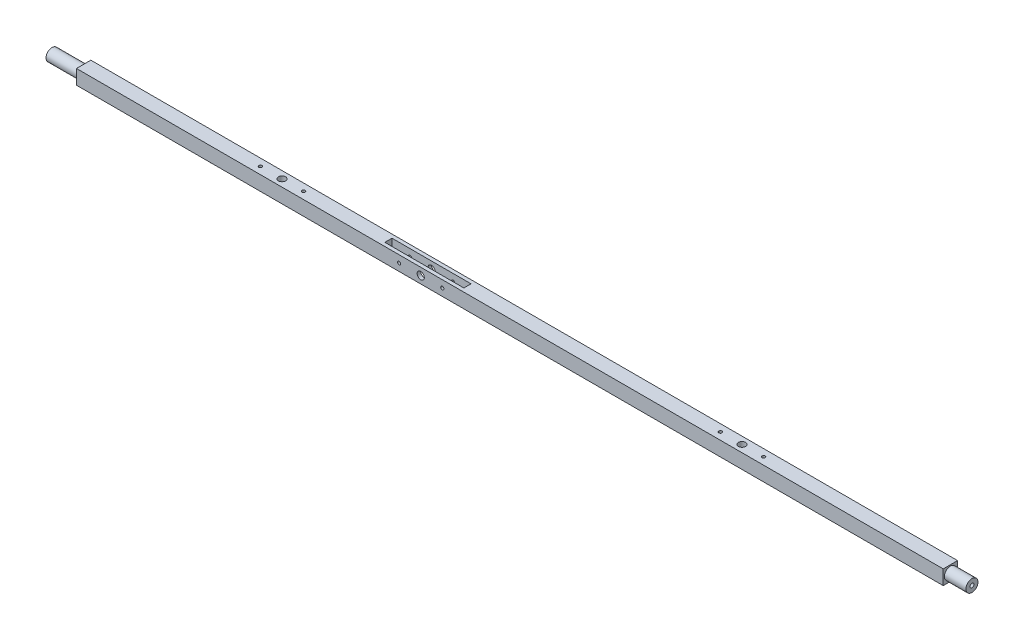
SolidWorks part; units mm, degrees
material "6061-T6 (SS)"
ref_plane "Front Plane" through (0, 0, 0) normal (0, 0, 1) x (1, 0, 0)
ref_plane "Top Plane" through (0, 0, 0) normal (0, 1, 0) x (1, 0, 0)
ref_plane "Right Plane" through (0, 0, 0) normal (1, 0, 0) x (0, 0, -1)
sketch "Sketch1" plane through (0, 0, 0) normal (1, 0, 0) x (0, 0, -1)
  line L1 (-6.35, -6.4107) -> (6.35, -6.4107)
  line L2 (-6.35, -6.4107) -> (-6.35, 6.4107)
  line L3 (-6.35, 6.4107) -> (6.35, 6.4107)
  line L4 (6.35, -6.4107) -> (6.35, 6.4107)
  line L5 (-6.35, -6.4107) -> (6.35, 6.4107) construction
  line L6 (-6.35, 6.4107) -> (6.35, -6.4107) construction
  point P0 (0, 0)
  dimension "D1" = 12.7
  dimension "D2" = 12.8213
extrude "Length" add sketch "Sketch1" along normal mid plane 812.8
ref_plane "Top" through (406.4, 0, 0) normal (1, 0, 0) x (0, 0, -1)
sketch "Sketch2" plane through (406.4, 0, 0) normal (1, 0, 0) x (0, 0, -1)
  line L5 (-3.7537, -3.7896) -> (2.2344, 2.2557) construction
  line L6 (-3.7537, 3.7896) -> (3.7537, -3.7896) construction
  line L7 (-6.35, -6.4107) -> (6.35, -6.4107)
  line L8 (-6.35, -6.4107) -> (-6.35, 6.4107)
  line L9 (-6.35, 6.4107) -> (6.35, 6.4107)
  line L10 (6.35, -6.4107) -> (6.35, 6.4107)
  line L11 (-6.35, -6.4107) -> (6.35, 6.4107) construction
  line L12 (-6.35, 6.4107) -> (6.35, -6.4107) construction
  circle A0 centre (0, 0) radius 5.334
  point P0 (0, 0)
  dimension "D1" = 10.668
extrude "Round Cut 1" cut sketch "Sketch2" against normal blind 19.05 contours L7 L10 L9 L8 A0
ref_plane "Bottom Plane" through (-406.4, 0, 0) normal (-1, 0, 0) x (0, 0, 1)
sketch "Sketch3" plane through (-406.4, 0, 0) normal (-1, 0, 0) x (0, 0, 1)
  line L1 (-6.35, -6.4107) -> (6.35, -6.4107)
  line L2 (-6.35, -6.4107) -> (-6.35, 6.4107)
  line L3 (-6.35, 6.4107) -> (6.35, 6.4107)
  line L4 (6.35, -6.4107) -> (6.35, 6.4107)
  line L5 (-6.35, -6.4107) -> (6.35, 6.4107) construction
  line L6 (-6.35, 6.4107) -> (6.35, -6.4107) construction
  circle A0 centre (0, 0) radius 5.334
  point P0 (0, 0)
  dimension "D1" = 10.668
extrude "Round Cut 2" cut sketch "Sketch3" against normal blind 27.94 contours L1 L4 L3 L2 A0
ref_plane "Plane13" through (0, -6.4107, 0) normal (0, -1, 0) x (-1, 0, 0)
sketch "Sketch9" plane through (0, -6.4107, 0) normal (0, -1, 0) x (-1, 0, 0)
  line L0 (-387.35, 6.35) -> (378.46, 6.35) construction
  line L1 (-279.4, 6.35) -> (-228.6, 6.35)
  line L2 (-279.4, 6.35) -> (-279.4, -6.35)
  line L3 (-279.4, -6.35) -> (-228.6, -6.35)
  line L4 (-228.6, 6.35) -> (-228.6, -6.35)
  line L5 (-387.35, -6.35) -> (378.46, -6.35) construction
  line L6 (-406.4, 5.8674) -> (-406.4, -5.8674) construction
  dimension "D1" = 50.8
  dimension "D2" = 127
sketch "Sketch10" plane through (0, -6.4107, 0) normal (0, -1, 0) x (-1, 0, 0)
  line L0 (406.4, -5.334) -> (406.4, 5.334) construction
  line L1 (50.8, -4.7642) -> (355.6, -4.7642)
  line L2 (50.8, -4.7642) -> (50.8, 4.6338)
  line L3 (50.8, 4.6338) -> (355.6, 4.6338)
  line L4 (355.6, -4.7642) -> (355.6, 4.6338)
  line L5 (50.8, -4.7642) -> (355.6, 4.6338) construction
  line L6 (50.8, 4.6338) -> (355.6, -4.7642) construction
  point P0 (203.2, -0.0652)
  dimension "D1" = 9.398
  dimension "D2" = 304.8
  dimension "D3" = 203.2
extrude "Cut-Extrude2" [suppressed] cut sketch "Sketch10" against normal blind 7.5438
ref_plane "Plane14" through (0, 0, 6.35) normal (0, 0, 1) x (1, 0, 0)
sketch "Sketch11" [suppressed] plane through (0, 0, 6.35) normal (0, 0, 1) x (1, 0, 0)
  line L0 (-50.8, 1.1331) -> (-355.6, 1.1331) construction
  line L1 (-355.6, 1.1331) -> (-355.6, -6.4107) construction
  line L2 (-349.25, -2.6769) -> (-63.4679, -2.6769) construction
  circle A0 centre (-349.25, -2.6769) radius 1.2573
  circle A1 centre (-336.55, -2.6769) radius 1.2573
  circle A2 centre (-323.85, -2.6769) radius 1.2573
  circle A3 centre (-311.15, -2.6769) radius 1.2573
  circle A4 centre (-298.45, -2.6769) radius 1.2573
  circle A5 centre (-285.75, -2.6769) radius 1.2573
  circle A6 centre (-273.05, -2.6769) radius 1.2573
  circle A7 centre (-260.35, -2.6769) radius 1.2573
  circle A8 centre (-247.65, -2.6769) radius 1.2573
  circle A9 centre (-234.95, -2.6769) radius 1.2573
  circle A10 centre (-222.25, -2.6769) radius 1.2573
  circle A11 centre (-209.55, -2.6769) radius 1.2573
  circle A12 centre (-196.85, -2.6769) radius 1.2573
  circle A13 centre (-184.15, -2.6769) radius 1.2573
  circle A14 centre (-171.45, -2.6769) radius 1.2573
  circle A15 centre (-158.75, -2.6769) radius 1.2573
  circle A16 centre (-146.05, -2.6769) radius 1.2573
  circle A17 centre (-133.35, -2.6769) radius 1.2573
  circle A18 centre (-120.65, -2.6769) radius 1.2573
  circle A19 centre (-107.95, -2.6769) radius 1.2573
  circle A20 centre (-95.25, -2.6769) radius 1.2573
  circle A21 centre (-82.55, -2.6769) radius 1.2573
  circle A22 centre (-69.85, -2.6769) radius 1.2573
  circle A23 centre (-57.15, -2.6769) radius 1.2573
  dimension "D1" = 2.5146
  dimension "D2" = 3.81
  dimension "D3" = 24
  dimension "25" = 6.35
extrude "Cut-Extrude3" [suppressed] cut sketch "Sketch11" against normal through all
sketch "Sketch12" plane through (0, -6.4107, 0) normal (0, -1, 0) x (-1, 0, 0)
  line L1 (0, 3.175) -> (-38.1, 3.175)
  line L2 (0, 3.175) -> (0, -3.175)
  line L3 (0, -3.175) -> (-38.1, -3.175)
  line L4 (-38.1, 3.175) -> (-38.1, -3.175)
  dimension "D1" = 38.1
  dimension "D2" = 6.35
  dimension "D3" = 3.175
  dimension "D4" = 0
extrude "Cut-Extrude4" [suppressed] cut sketch "Sketch12" against normal blind 6.35
sketch "Sketch13" [suppressed] plane through (0, 0, 6.35) normal (0, 0, 1) x (1, 0, 0)
  line L0 (0, -0.0607) -> (0, -6.4107) construction
  line L1 (378.46, -6.4107) -> (-378.46, -6.4107) construction
  circle A0 centre (5.08, -3.2357) radius 1.2573
  circle A1 centre (13.97, -3.2357) radius 1.2573
  circle A2 centre (22.86, -3.2357) radius 1.2573
  circle A3 centre (31.75, -3.2357) radius 1.2573
  dimension "D1" = 2.5146
  dimension "D3" = 5.08
  dimension "D4" = 3.175
  dimension "D2" = 4
extrude "Cut-Extrude5" [suppressed] cut sketch "Sketch13" against normal through all
sketch "Sketch14" plane through (406.4, 0, 0) normal (1, 0, 0) x (0, 0, -1)
  circle A0 centre (0, 0) radius 1.7526
  dimension "D1" = 3.5052
extrude "Cut-Extrude6" cut sketch "Sketch14" against normal blind 12.7
sketch "Sketch15" plane through (-406.4, 0, 0) normal (-1, 0, 0) x (0, 0, 1)
  circle A0 centre (0, 0) radius 1.7526
  dimension "D1" = 3.5052
extrude "Cut-Extrude7" cut sketch "Sketch15" against normal blind 19.05
ref_plane "Plane15" through (0, 6.4107, 0) normal (0, 1, 0) x (1, 0, 0)
sketch "Bottom Washer" plane through (0, 6.4107, 0) normal (0, 1, 0) x (1, 0, 0)
  circle A1 centre (-222.25, 0) radius 1.4224
  circle A2 centre (-184.15, 0) radius 1.4224
  dimension "D4" = 2.8448
  dimension "D5" = 2.8448
extrude "Bottom washer bolts" cut sketch "Bottom Washer" against normal blind 10.922 contours A1 | A2
sketch "Sketch18" plane through (0, 6.4107, 0) normal (0, 1, 0) x (1, 0, 0)
  line L0 (-406.4, 5.334) -> (-406.4, -5.334) construction
  circle A0 centre (-203.2, 0) radius 3.175
  dimension "D1" = 6.35
  dimension "D2" = 203.2
extrude "Bottom Washer Center Bolt" cut sketch "Sketch18" against normal up to next
sketch "Sketch17" plane through (0, 6.4107, 0) normal (0, 1, 0) x (1, 0, 0)
  line L0 (406.4, -5.334) -> (406.4, 5.334) construction
  circle A0 centre (203.2, 0) radius 3.175
  dimension "D1" = 6.35
  dimension "D2" = 203.2
extrude "Top Washer Center Bolt" cut sketch "Sketch17" against normal up to next
sketch "Sketch16" plane through (0, 6.4107, 0) normal (0, 1, 0) x (1, 0, 0)
  circle A1 centre (222.25, 0) radius 1.4224
  circle A2 centre (184.15, 0) radius 1.4224
  dimension "D1" = 38.1
  dimension "D3" = 2.8448
  dimension "D4" = 2.8448
extrude "Top Washer" cut sketch "Sketch16" against normal blind 10.922
ref_plane "Plane16" through (0, -6.4107, 0) normal (0, -1, 0) x (-1, 0, 0)
sketch "Sketch19" plane through (0, -6.4107, 0) normal (0, -1, 0) x (-1, 0, 0)
  line L0 (-387.35, 6.35) -> (378.46, 6.35) construction
  line L1 (39.3606, 3.175) -> (109.2106, 3.175)
  line L2 (39.3606, 3.175) -> (39.3606, -3.175)
  line L3 (39.3606, -3.175) -> (109.2106, -3.175)
  line L4 (109.2106, 3.175) -> (109.2106, -3.175)
  dimension "D1" = 6.35
  dimension "D2" = 3.175
  dimension "D3" = 69.85
extrude "Cut-Extrude8" cut sketch "Sketch19" against normal through all
ref_plane "Plane17" through (0, 0, 6.35) normal (0, 0, 1) x (1, 0, 0)
sketch "Sketch20" plane through (0, 0, 6.35) normal (0, 0, 1) x (1, 0, 0)
  line L1 (-39.3606, 6.4107) -> (-39.3606, -6.4107) construction
  line L2 (-109.2106, 6.4107) -> (-109.2106, -6.4107) construction
  circle A0 centre (-93.3356, 0) radius 1.397
  circle A1 centre (-74.2856, 0) radius 3.175
  circle A2 centre (-55.2356, 0) radius 1.397
  dimension "D1" = 2.794
  dimension "D2" = 6.35
  dimension "D3" = 2.794
  dimension "D4" = 15.875
  dimension "D5" = 15.875
  dimension "D6" = 19.05
extrude "Cut-Extrude9" cut sketch "Sketch20" against normal through all
equation "\"Diameter\"= .420"
equation "\"Round Cut Depth Top\"= .75"
equation "\"Stringer Length\"= 32"
equation "\"D1@Sketch3\"= \"Diameter\""
equation "\"D1@Sketch2\"= \"Diameter\""
equation "\"D1@Round Cut 1\"= \"Round Cut Depth Top\""
equation "\"D1@Round Cut 2\" = \"Round Cut Depth Bottom\""
equation "\"D1@Length\"= \"Stringer Length\""
equation "\"Round Cut Depth Bottom\"= 1.1"
